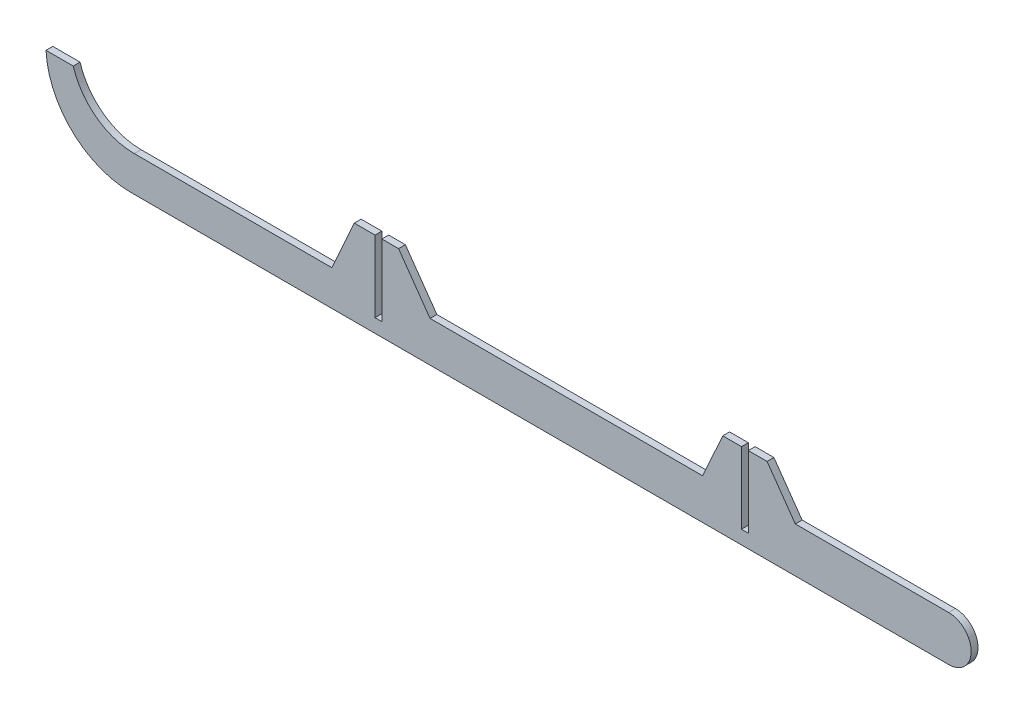
SolidWorks part; units mm, degrees
material "Plástico personalizado"
ref_plane "Plano frontal" through (0, 0, 0) normal (0, 0, 1) x (1, 0, 0)
ref_plane "Plano superior" through (0, 0, 0) normal (0, 1, 0) x (1, 0, 0)
ref_plane "Plano direito" through (0, 0, 0) normal (1, 0, 0) x (0, 0, -1)
sketch "Esboço1" plane through (0, 0, 0) normal (0, 0, 1) x (1, 0, 0)
  line L0 (78.9077, 0) -> (-161.0923, 0)
  line L1 (-102.1286, 10.3707) -> (-160.1286, 10.3707)
  line L2 (-186.014, 23.6714) -> (-178.014, 23.6714)
  line L3 (-102.1286, 10.3707) -> (-95.5355, 25)
  line L4 (-82.5355, 25) -> (-87.442, 25)
  line L5 (-82.5355, 25) -> (-73.2914, 11.8839)
  line L6 (-73.2914, 11.8839) -> (6.7086, 11.8839)
  line L7 (6.7086, 11.8839) -> (12.6198, 25)
  line L8 (12.6198, 25) -> (18.1198, 25)
  line L9 (25.6198, 25) -> (33.9077, 13.2405)
  line L10 (33.9077, 13.2405) -> (78.9077, 13.2405)
  line L11 (-89.442, 25) -> (-95.5355, 25)
  line L12 (20.1198, 25) -> (25.6198, 25)
  line L13 (-89.442, 25) -> (-89.442, 4)
  line L14 (-89.442, 4) -> (-87.442, 4)
  line L15 (-87.442, 25) -> (-87.442, 4)
  line L19 (18.1198, 25) -> (18.1198, 4)
  line L20 (18.1198, 4) -> (20.1198, 4)
  line L21 (20.1198, 25) -> (20.1198, 4)
  arc A0 (-161.0923, 0) -> (-186.014, 23.6714) centre (-161.0923, 24.9547) cw
  arc A1 (-160.1286, 10.3707) -> (-178.014, 23.6714) centre (-160.1286, 29.0463) cw
  arc A2 (78.9077, 13.2405) -> (78.9077, 0) centre (78.9077, 6.6202) cw
  point P17 (-88.442, 26.1695)
  point P22 (19.1198, 28.116)
  dimension "D3" = 13
  dimension "D1" = 240
  dimension "D2" = 45
  dimension "D4" = 13
  dimension "D5" = 80
  dimension "D6" = 58
  dimension "D7" = 8
  dimension "D8" = 4
  dimension "D9" = 4
  dimension "D10" = 2
  dimension "D11" = 2
  dimension "D12" = 21
  dimension "D13" = 21
extrude "Ressalto-extrusão1" add sketch "Esboço1" along normal blind 2
